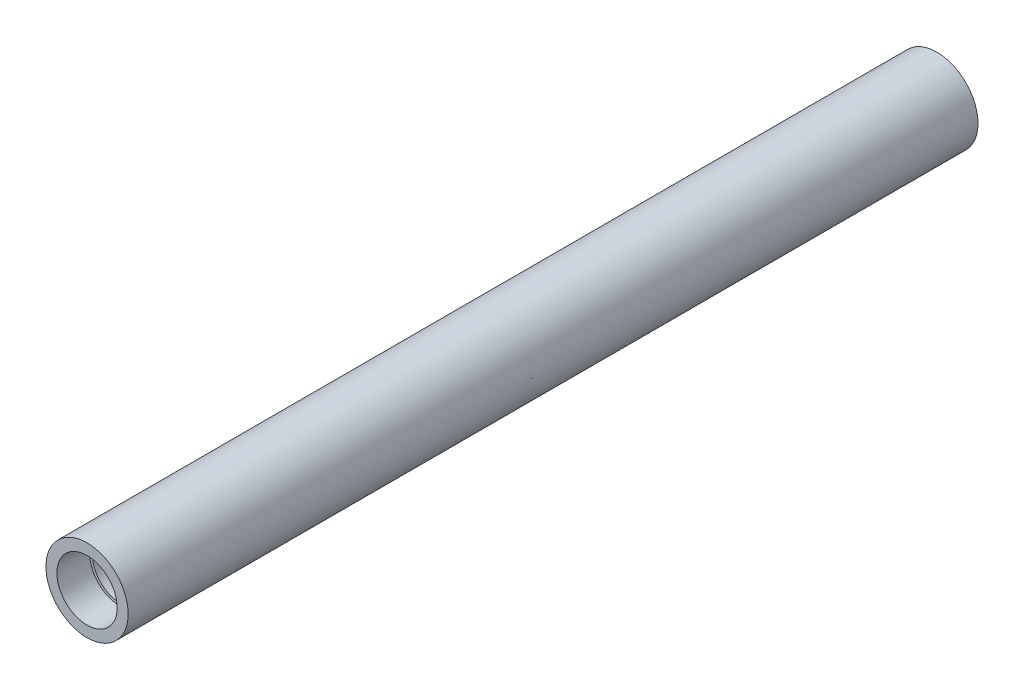
SolidWorks part; units mm, degrees
ref_plane "Plan de face" through (0, 0, 0) normal (0, 0, 1) x (1, 0, 0)
ref_plane "Plan de dessus" through (0, 0, 0) normal (0, 1, 0) x (1, 0, 0)
ref_plane "Plan de droite" through (0, 0, 0) normal (1, 0, 0) x (0, 0, -1)
sketch "Esquisse1" plane through (0, 0, 0) normal (0, 0, 1) x (1, 0, 0)
  circle A0 centre (0, 0) radius 15
  circle A1 centre (0, 0) radius 10
  dimension "D1" = 30
  dimension "D2" = 20
extrude "Boss.-Extru.1" add sketch "Esquisse1" along normal blind 310
sketch "Esquisse2" plane through (0, 0, 0) normal (0, 0, -1) x (-1, 0, 0)
  circle A0 centre (0, 0) radius 13
  circle A1 centre (0, 0) radius 10
extrude "Enlèv. mat.-Extru.1" cut sketch "Esquisse2" against normal blind 7
sketch "Esquisse3" plane through (0, 0, 310) normal (0, 0, 1) x (1, 0, 0)
  circle A0 centre (0, 0) radius 11
  circle A1 centre (0, 0) radius 11
  circle A2 centre (0, 0) radius 10
  circle M2 centre (0, 0) radius 10
extrude "Enlèv. mat.-Extru.2" cut sketch "Esquisse3" against normal blind 12 contours A0 M2
